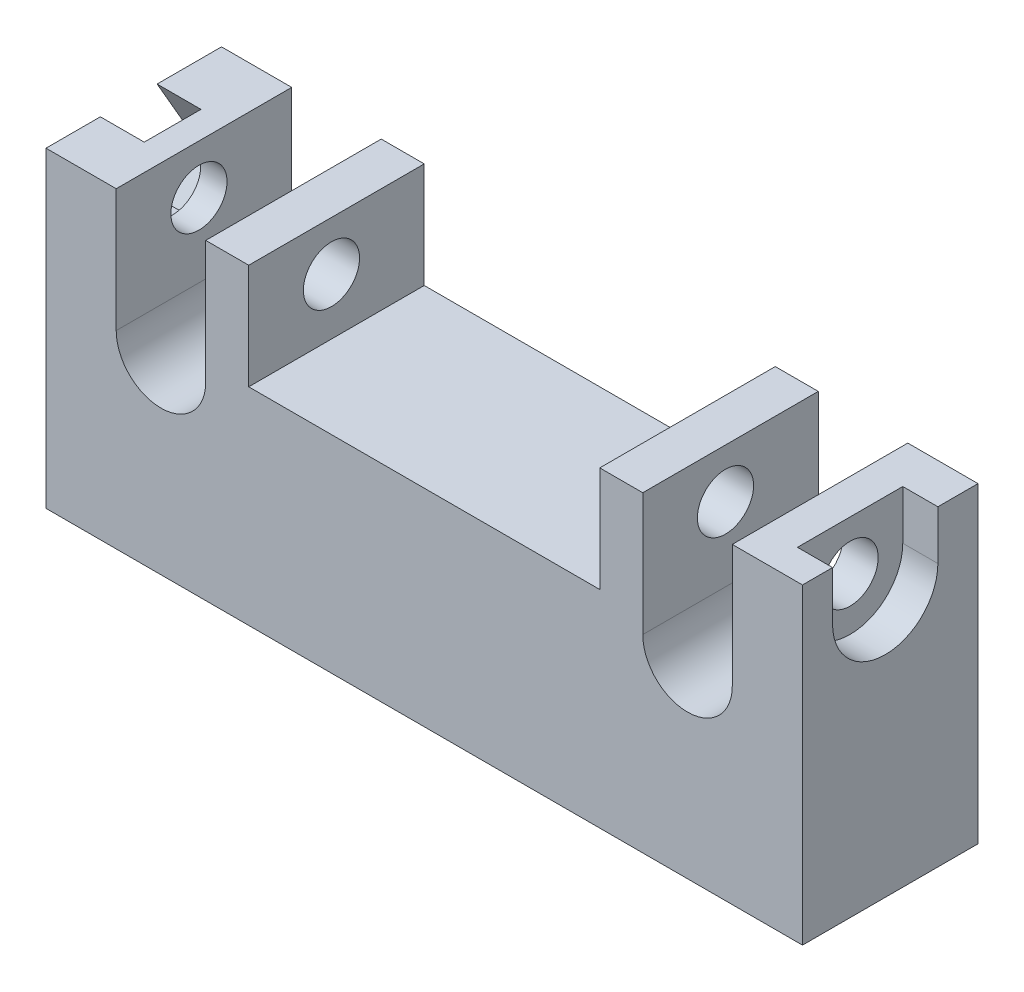
SolidWorks part; units mm, degrees
ref_plane "Front Plane" through (0, 0, 0) normal (0, 0, 1) x (1, 0, 0)
ref_plane "Top Plane" through (0, 0, 0) normal (0, 1, 0) x (1, 0, 0)
ref_plane "Right Plane" through (0, 0, 0) normal (1, 0, 0) x (0, 0, -1)
sketch "Sketch1" plane through (0, 0, 0) normal (0, 0, 1) x (1, 0, 0)
  line L0 (-21.55, 7.2) -> (-17.55, 7.2)
  line L1 (-17.55, 7.2) -> (-17.55, 0.2)
  line L2 (-12.45, 0.2) -> (-12.45, 7.2)
  line L3 (-12.45, 7.2) -> (12.45, 7.2)
  line L4 (12.45, 7.2) -> (12.45, 0.2)
  line L5 (17.55, 0.2) -> (17.55, 7.2)
  line L6 (17.55, 7.2) -> (21.55, 7.2)
  line L7 (21.55, 7.2) -> (21.55, -10.5744)
  line L8 (21.55, -10.5744) -> (-21.55, -10.5744)
  line L9 (-21.55, -10.5744) -> (-21.55, 7.2)
  arc A0 (-17.55, 0.2) -> (-12.45, 0.2) centre (-15, 0.2) ccw
  arc A1 (12.45, 0.2) -> (17.55, 0.2) centre (15, 0.2) ccw
  point P10 (-10.2, -4.68)
  point P15 (0, 0)
  point P16 (28.5518, -10.5744)
  point P17 (0, 7.2)
  dimension "D1" = 2.55
  dimension "D2" = 7
  dimension "D3" = 30
  dimension "D4" = 4
extrude "Boss-Extrude1" add sketch "Sketch1" along normal blind 10
sketch "Sketch2" plane through (21.55, 0, 0) normal (1, 0, 0) x (0, 0, -1)
  line L0 (-10, 7.2) -> (0, 7.2) construction
  line L3 (0, 4.4) -> (-5.2864, 4.4) construction
  line L4 (-5.2864, 7.2) -> (-5.2864, 4.4) construction
  line L6 (-10, 0.2) -> (0, 0.2) construction
  line L7 (-10, 0.2) -> (0, 0.2) construction
  circle A0 centre (-5.2864, 4.4) radius 1.6
  point P5 (-4.9943, 3.8666)
  point P6 (-9.4666, 3.2953)
  point P7 (-9.2466, 7.2)
  point P10 (-9.5137, 3.4)
  point P13 (-5.2864, 3.4)
  dimension "D1" = 3.2
  dimension "D2" = 4.2
extrude "Cut-Extrude1" cut sketch "Sketch2" against normal through all
sketch "Sketch3" plane through (21.55, 0, 0) normal (1, 0, 0) x (0, 0, -1)
  line L0 (-8.2864, 7.2) -> (-2.2864, 7.2)
  line L1 (-10, 7.2) -> (0, 7.2) construction
  line L2 (-2.2864, 7.2) -> (-2.2864, 4.4)
  line L3 (-8.2864, 4.4) -> (-8.2864, 7.2)
  circle A0 centre (-5.2864, 4.4) radius 1.6 construction
  circle A1 centre (-5.2864, 4.4) radius 1.6 construction
  arc A3 (-2.2864, 4.4) -> (-8.2864, 4.4) centre (-5.2864, 4.4) cw
  point P10 (-5.1686, 4.6871)
  dimension "D1" = 6
extrude "Cut-Extrude2" cut sketch "Sketch3" against normal blind 2
sketch "Sketch4" plane through (-21.55, 0, 0) normal (-1, 0, 0) x (0, 0, 1)
  line L1 (8.5196, 4.4) -> (6.903, 7.2)
  line L2 (6.903, 7.2) -> (3.6699, 7.2)
  line L3 (3.6699, 7.2) -> (2.0533, 4.4)
  line L4 (2.0533, 4.4) -> (3.6699, 1.6)
  line L5 (3.6699, 1.6) -> (6.903, 1.6)
  line L6 (6.903, 1.6) -> (8.5196, 4.4)
  circle A0 centre (5.2864, 4.4) radius 2.8 construction
  circle A1 centre (5.2864, 4.4) radius 1.6 construction
  circle A2 centre (5.2864, 4.4) radius 1.6 construction
  dimension "D1" = 5.6
extrude "Cut-Extrude3" cut sketch "Sketch4" against normal blind 2.5
sketch "Sketch6" plane through (0, 0, 10) normal (0, 0, 1) x (1, 0, 0)
  line L0 (12.45, 7.2) -> (-12.45, 7.2) construction
  line L1 (-10, 7.2) -> (10, 7.2)
  line L2 (-10, 7.2) -> (-10, 1.2)
  line L3 (-10, 1.2) -> (10, 1.2)
  line L4 (10, 7.2) -> (10, 1.2)
  point P6 (0, 7.2)
  dimension "D1" = 20
  dimension "D2" = 6
extrude "Cut-Extrude4" cut sketch "Sketch6" against normal through all
